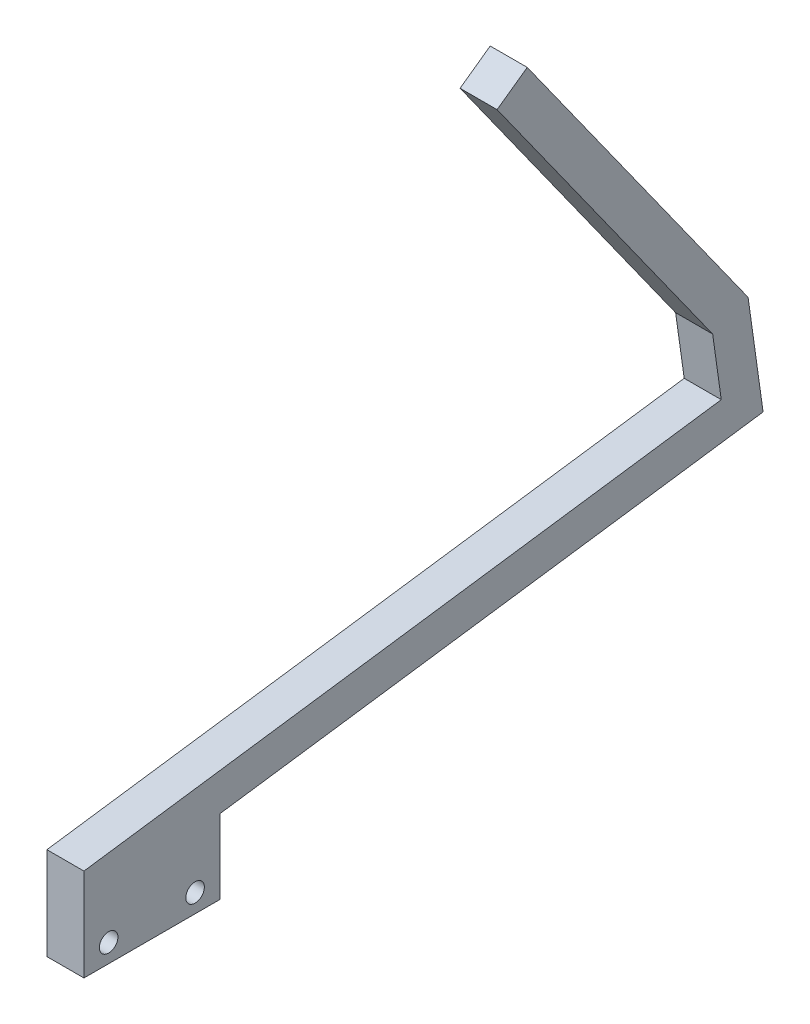
SolidWorks part; units mm, degrees
ref_plane "Front Plane" through (0, 0, 0) normal (0, 0, 1) x (1, 0, 0)
ref_plane "Top Plane" through (0, 0, 0) normal (0, 1, 0) x (1, 0, 0)
ref_plane "Right Plane" through (0, 0, 0) normal (1, 0, 0) x (0, 0, -1)
sketch "Sketch1" plane through (0, 0, 0) normal (1, 0, 0) x (0, 0, -1)
  line L0 (0, 0) -> (0, 15)
  line L1 (0, 15) -> (103.2234, 29.5071)
  line L2 (103.2234, 29.5071) -> (101.8316, 39.4098)
  line L3 (101.8316, 39.4098) -> (66.9165, 88.3456)
  line L4 (107.5688, 41.6991) -> (110, 24.4005)
  line L5 (110, 24.4005) -> (22, 12.0329)
  line L6 (22, 12.0329) -> (22, 0)
  line L7 (22, 0) -> (0, 0)
  line L8 (66.9165, 88.3456) -> (71.8008, 91.8304)
  line L9 (71.8008, 91.8304) -> (107.5688, 41.6991)
  circle A0 centre (4, 3) radius 1.5
  circle A1 centre (18, 3) radius 1.5
  dimension "D9" = 3
  dimension "D1" = 8
  dimension "D2" = 15
  dimension "D3" = 6
  dimension "D4" = 6
  dimension "D5" = 22
  dimension "D6" = 110
  dimension "D7" = 10
  dimension "D8" = 6
  dimension "D10" = 4
  dimension "D11" = 4
  dimension "D12" = 3
extrude "Boss-Extrude1" add sketch "Sketch1" along normal blind 6
